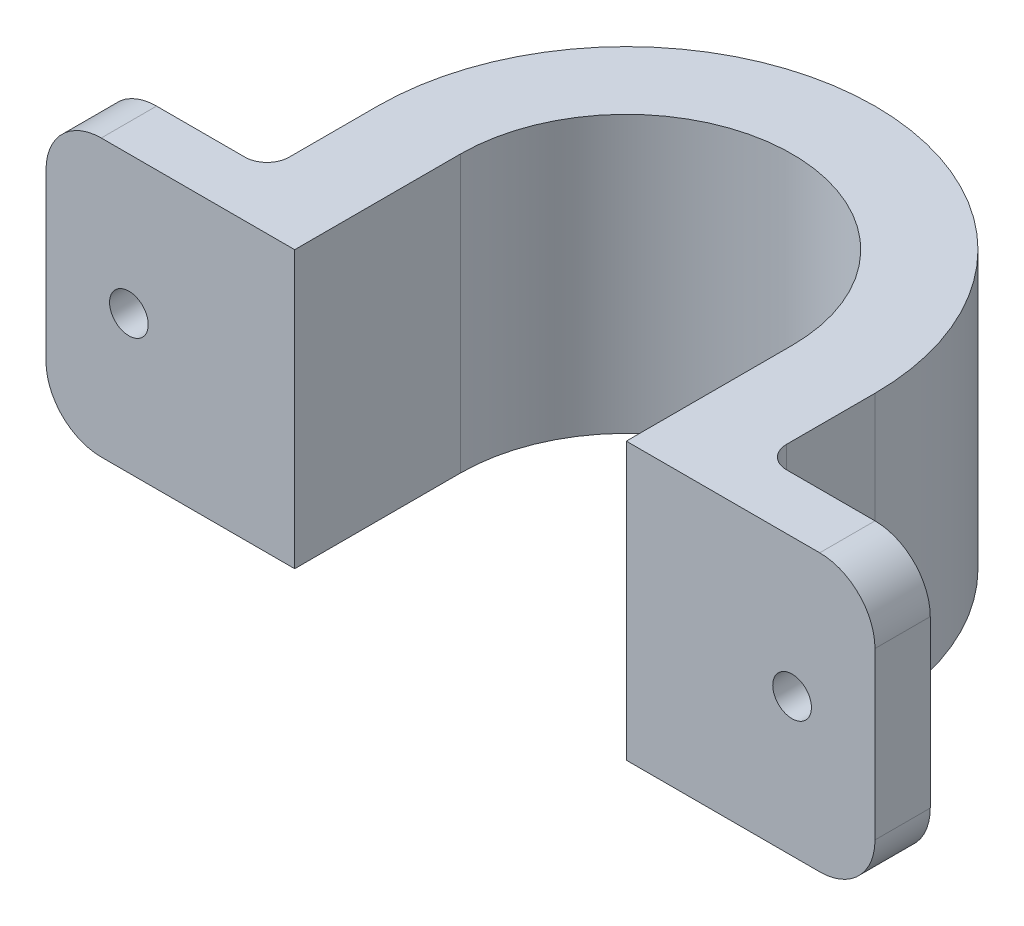
SolidWorks part; units mm, degrees
ref_plane "Front Plane" through (0, 0, 0) normal (0, 0, 1) x (1, 0, 0)
ref_plane "Top Plane" through (0, 0, 0) normal (0, 1, 0) x (1, 0, 0)
ref_plane "Right Plane" through (0, 0, 0) normal (1, 0, 0) x (0, 0, -1)
sketch "Sketch1" plane through (0, 0, 0) normal (0, 1, 0) x (1, 0, 0)
  line L0 (-7.5, 0) -> (-7.5, -10)
  line L1 (-7.5, -10) -> (-22.5, -10)
  line L2 (-22.5, -10) -> (-22.5, -15)
  line L3 (-22.5, -15) -> (0, -15)
  line L4 (0, -15) -> (0, 0)
  line L5 (-7.5, 0) -> (0, 0) construction
  line L6 (15, 0) -> (30, 0) construction
  line L7 (30, 0) -> (37.5, 0) construction
  line L8 (0, 0) -> (15, 0) construction
  line L9 (30, 0) -> (30, -15)
  line L10 (30, -15) -> (52.5, -15)
  line L11 (52.5, -15) -> (52.5, -10)
  line L12 (52.5, -10) -> (37.5, -10)
  line L13 (37.5, -10) -> (37.5, 0)
  arc A0 (-7.5, 0) -> (37.5, 0) centre (15, 0) cw
  arc A1 (0, 0) -> (30, 0) centre (15, 0) cw
  dimension "D1" = 15
  dimension "D2" = 7.5
  dimension "D3" = 5
  dimension "D4" = 15
  dimension "D5" = 15
extrude "Boss-Extrude1" add sketch "Sketch1" along normal blind 25
sketch "Sketch4" plane through (0, 0, 10) normal (0, 0, -1) x (-1, 0, 0)
  line L0 (-52.5, 12.5) -> (-37.5, 12.5) construction
  line L1 (-52.5, 25) -> (-52.5, 0) construction
  line L2 (-37.5, 25) -> (-37.5, 0) construction
  line L3 (-15, 25) -> (-15, 0) construction
  line L4 (7.5, 25) -> (-37.5, 25) construction
  line L5 (-37.5, 0) -> (7.5, 0) construction
  circle A0 centre (-45, 12.5) radius 1.75
  circle A1 centre (15, 12.5) radius 1.75
  dimension "D1" = 3.5
  dimension "D2" = 30
extrude "Cut-Extrude1" cut sketch "Sketch4" against normal through all
fillet "Fillet1" radius 5 4 edges at (52.5, 25, 12.5) (52.5, 0, 12.5) (-22.5, 25, 12.5) (-22.5, 0, 12.5)
fillet "Fillet2" radius 2 2 edges at (37.5, 12.5, 10) (-7.5, 12.5, 10)
equation "\"D5@Sketch1\" = \"Diamter\" / 2"
equation "\"D1@Sketch1\" = \"Diamter\" / 2"
equation "\"Diamter\"= 30"
